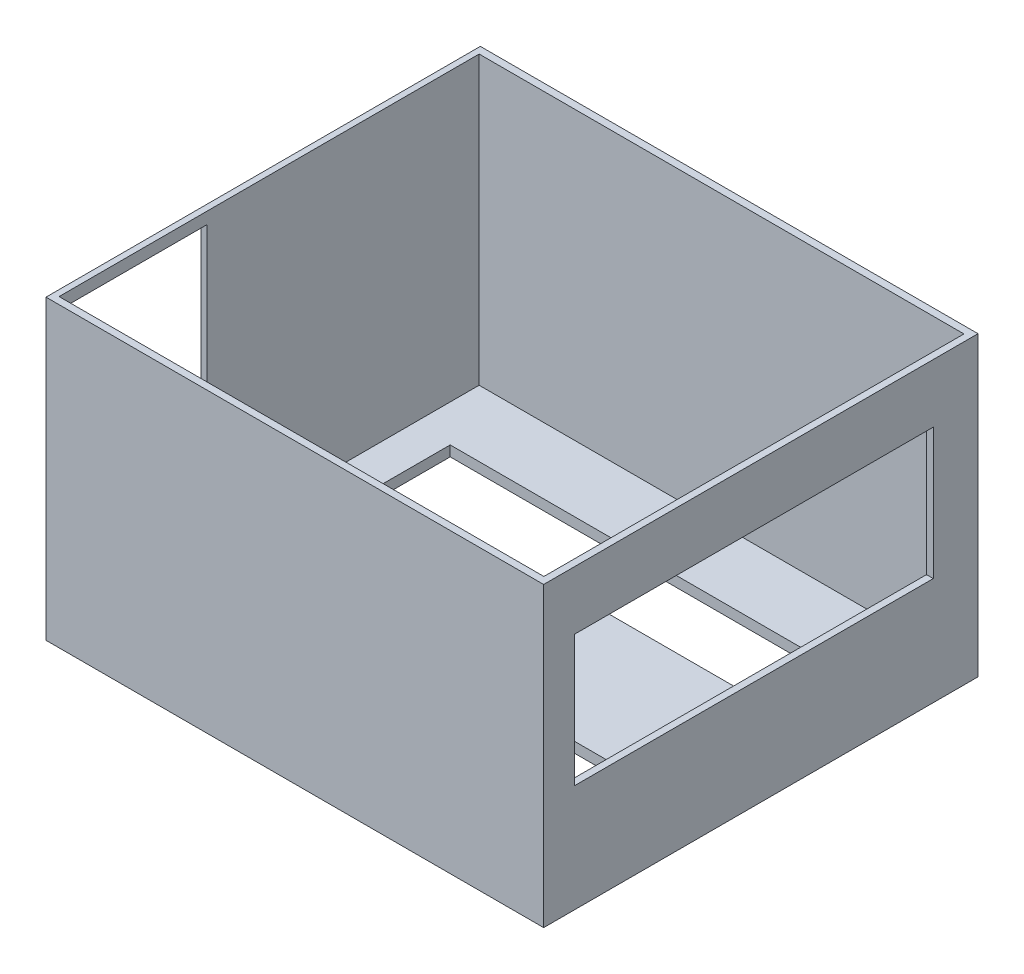
SolidWorks part; units mm, degrees
ref_plane "Front Plane" through (0, 0, 0) normal (0, 0, 1) x (1, 0, 0)
ref_plane "Top Plane" through (0, 0, 0) normal (0, 1, 0) x (1, 0, 0)
ref_plane "Right Plane" through (0, 0, 0) normal (1, 0, 0) x (0, 0, -1)
sketch "Sketch1" plane through (0, 0, 0) normal (0, 1, 0) x (1, 0, 0)
  line L1 (-72.9004, 81.3487) -> (71.0996, 81.3487)
  line L2 (-72.9004, 81.3487) -> (-72.9004, -44.3313)
  line L3 (-72.9004, -44.3313) -> (71.0996, -44.3313)
  line L4 (71.0996, 81.3487) -> (71.0996, -44.3313)
extrude "Boss-Extrude1" add sketch "Sketch1" along normal blind 3
sketch "Sketch2" plane through (0, 3, 0) normal (0, 1, 0) x (1, 0, 0)
  line L1 (-72.9004, 81.3487) -> (71.0996, 81.3487)
  line L2 (-72.9004, 81.3487) -> (-72.9004, -44.3313)
  line L3 (-72.9004, -44.3313) -> (71.0996, -44.3313)
  line L4 (71.0996, 81.3487) -> (71.0996, -44.3313)
  line L5 (-71.1533, 79.2527) -> (69.1292, 79.2527)
  line L6 (-71.1533, 79.2527) -> (-71.1533, -42.2955)
  line L7 (-71.1533, -42.2955) -> (69.1292, -42.2955)
  line L8 (69.1292, 79.2527) -> (69.1292, -42.2955)
extrude "Boss-Extrude2" add sketch "Sketch2" along normal blind 83
sketch "Sketch4" plane through (71.0996, 0, 0) normal (1, 0, 0) x (0, 0, -1)
  line L1 (68.4082, 69.0566) -> (-35.3386, 69.0566)
  line L2 (68.4082, 69.0566) -> (68.4082, 31.1026)
  line L3 (68.4082, 31.1026) -> (-35.3386, 31.1026)
  line L4 (-35.3386, 69.0566) -> (-35.3386, 31.1026)
extrude "Cut-Extrude1" cut sketch "Sketch4" against normal blind 20
sketch "Sketch5" plane through (0, 0, 0) normal (0, -1, 0) x (1, 0, 0)
  line L1 (50.3282, -60.1132) -> (-60.3856, -60.1132)
  line L2 (50.3282, -60.1132) -> (50.3282, -40.6984)
  line L3 (50.3282, -40.6984) -> (-60.3856, -40.6984)
  line L4 (-60.3856, -60.1132) -> (-60.3856, -40.6984)
  line L5 (50.3282, -3.8287) -> (-60.3856, -3.8287)
  line L6 (50.3282, -3.8287) -> (50.3282, 20.1928)
  line L7 (50.3282, 20.1928) -> (-60.3856, 20.1928)
  line L8 (-60.3856, -3.8287) -> (-60.3856, 20.1928)
extrude "Cut-Extrude2" cut sketch "Sketch5" against normal blind 20
sketch "Sketch6" plane through (-72.9004, 0, 0) normal (-1, 0, 0) x (0, 0, 1)
  line L1 (-0.5419, 6.9674) -> (39.2483, 6.9674)
  line L2 (-0.5419, 6.9674) -> (-0.5419, 82.619)
  line L3 (-0.5419, 82.619) -> (39.2483, 82.619)
  line L4 (39.2483, 6.9674) -> (39.2483, 82.619)
extrude "Cut-Extrude3" cut sketch "Sketch6" against normal blind 20
